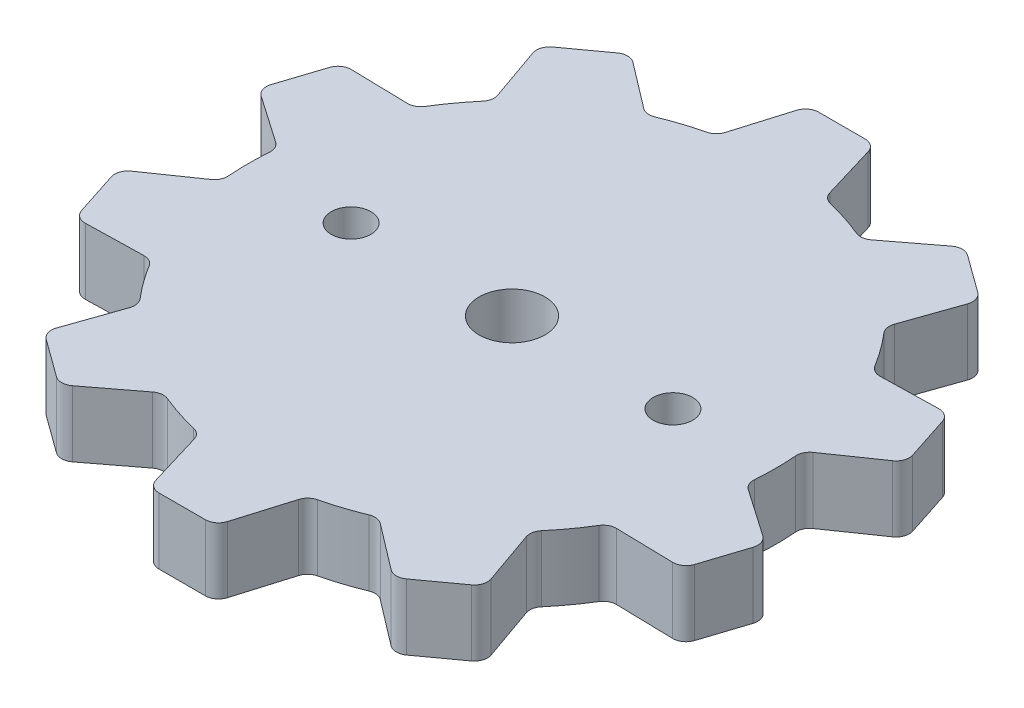
SolidWorks part; units mm, degrees
ref_plane "Front Plane" through (0, 0, 0) normal (0, 0, 1) x (1, 0, 0)
ref_plane "Top Plane" through (0, 0, 0) normal (0, 1, 0) x (1, 0, 0)
ref_plane "Right Plane" through (0, 0, 0) normal (1, 0, 0) x (0, 0, -1)
sketch "Sketch1" plane through (0, 0, 0) normal (0, 1, 0) x (1, 0, 0)
  line L0 (12.6721, 21.6949) -> (8.5196, 18.5315)
  line L1 (0, 25) -> (-2.5, 25)
  line L2 (0, 25) -> (2.5, 25)
  line L3 (14.6946, 20.2254) -> (12.6721, 21.6949)
  line L4 (14.6946, 20.2254) -> (16.7172, 18.756)
  line L5 (-2.5, 25) -> (-4, 20)
  line L6 (2.5, 25) -> (4, 20)
  line L7 (-4, 20) -> (-4.1293, 19.5691)
  line L8 (16.7172, 18.756) -> (14.9918, 13.8292)
  line L9 (14.9918, 13.8292) -> (14.8431, 13.4046)
  line L10 (4, 20) -> (4.1293, 19.5691)
  line L11 (8.5196, 18.5315) -> (8.1618, 18.2588)
  line L12 (23.0039, 10.1031) -> (17.7851, 9.9846)
  line L13 (23.7764, 7.7254) -> (23.0039, 10.1031)
  line L14 (23.7764, 7.7254) -> (24.549, 5.3478)
  line L15 (24.549, 5.3478) -> (20.2572, 2.3761)
  line L16 (20.2572, 2.3761) -> (19.8873, 2.12)
  line L17 (17.7851, 9.9846) -> (17.3353, 9.9744)
  line L18 (24.549, -5.3478) -> (20.2572, -2.3761)
  line L19 (23.7764, -7.7254) -> (24.549, -5.3478)
  line L20 (23.7764, -7.7254) -> (23.0039, -10.1031)
  line L21 (23.0039, -10.1031) -> (17.7851, -9.9846)
  line L22 (17.7851, -9.9846) -> (17.3353, -9.9744)
  line L23 (20.2572, -2.3761) -> (19.8873, -2.12)
  line L24 (16.7172, -18.756) -> (14.9918, -13.8292)
  line L25 (14.6946, -20.2254) -> (16.7172, -18.756)
  line L26 (14.6946, -20.2254) -> (12.6721, -21.6949)
  line L27 (12.6721, -21.6949) -> (8.5196, -18.5315)
  line L28 (8.5196, -18.5315) -> (8.1618, -18.2588)
  line L29 (14.9918, -13.8292) -> (14.8431, -13.4046)
  line L30 (2.5, -25) -> (4, -20)
  line L31 (0, -25) -> (2.5, -25)
  line L32 (0, -25) -> (-2.5, -25)
  line L33 (-2.5, -25) -> (-4, -20)
  line L34 (-4, -20) -> (-4.1293, -19.5691)
  line L35 (4, -20) -> (4.1293, -19.5691)
  line L36 (-12.6721, -21.6949) -> (-8.5196, -18.5315)
  line L37 (-14.6946, -20.2254) -> (-12.6721, -21.6949)
  line L38 (-14.6946, -20.2254) -> (-16.7172, -18.756)
  line L39 (-16.7172, -18.756) -> (-14.9918, -13.8292)
  line L40 (-14.9918, -13.8292) -> (-14.8431, -13.4046)
  line L41 (-8.5196, -18.5315) -> (-8.1618, -18.2588)
  line L42 (-23.0039, -10.1031) -> (-17.7851, -9.9846)
  line L43 (-23.7764, -7.7254) -> (-23.0039, -10.1031)
  line L44 (-23.7764, -7.7254) -> (-24.549, -5.3478)
  line L45 (-24.549, -5.3478) -> (-20.2572, -2.3761)
  line L46 (-20.2572, -2.3761) -> (-19.8873, -2.12)
  line L47 (-17.7851, -9.9846) -> (-17.3353, -9.9744)
  line L48 (-24.549, 5.3478) -> (-20.2572, 2.3761)
  line L49 (-23.7764, 7.7254) -> (-24.549, 5.3478)
  line L50 (-23.7764, 7.7254) -> (-23.0039, 10.1031)
  line L51 (-23.0039, 10.1031) -> (-17.7851, 9.9846)
  line L52 (-17.7851, 9.9846) -> (-17.3353, 9.9744)
  line L53 (-20.2572, 2.3761) -> (-19.8873, 2.12)
  line L54 (-16.7172, 18.756) -> (-14.9918, 13.8292)
  line L55 (-14.6946, 20.2254) -> (-16.7172, 18.756)
  line L56 (-14.6946, 20.2254) -> (-12.6721, 21.6949)
  line L57 (-12.6721, 21.6949) -> (-8.5196, 18.5315)
  line L58 (-8.5196, 18.5315) -> (-8.1618, 18.2588)
  line L59 (-14.9918, 13.8292) -> (-14.8431, 13.4046)
  circle A0 centre (0, 0) radius 20
  circle A1 centre (0, 0) radius 20
  circle A2 centre (0, 0) radius 20
  circle A3 centre (0, 0) radius 20
  circle A4 centre (0, 0) radius 20
  circle A5 centre (0, 0) radius 20
  circle A6 centre (0, 0) radius 20
  circle A7 centre (0, 0) radius 20
  circle A8 centre (0, 0) radius 20
  circle A9 centre (0, 0) radius 20
  point P93 (0, 0)
  dimension "D1" = 10
extrude "Boss-Extrude1" add sketch "Sketch1" along normal blind 5
sketch "Sketch2" plane through (0, 5, 0) normal (0, 1, 0) x (1, 0, 0)
  circle A0 centre (0, 0) radius 2.5
extrude "Cut-Extrude1" cut sketch "Sketch2" against normal blind 5
fillet "Fillet1" radius 1 20 edges at (-4.1293, 2.5, 19.5691) (-8.1618, 2.5, 18.2588) (-14.8431, 2.5, 13.4046) (-17.3353, 2.5, 9.9744) (-19.8873, 2.5, 2.12) (-19.8873, 2.5, -2.12) (-17.3353, 2.5, -9.9744) (-14.8431, 2.5, -13.4046) (-8.1618, 2.5, -18.2588) (-4.1293, 2.5, -19.5691) (4.1293, 2.5, -19.5691) (8.1618, 2.5, -18.2588) (14.8431, 2.5, -13.4046) (17.3353, 2.5, -9.9744) (19.8873, 2.5, -2.12) (19.8873, 2.5, 2.12) (17.3353, 2.5, 9.9744) (14.8431, 2.5, 13.4046) (8.1618, 2.5, 18.2588) (4.1293, 2.5, 19.5691)
fillet "Fillet2" radius 1 20 edges at (-12.6721, 2.5, 21.6949) (-16.7172, 2.5, 18.756) (-23.0039, 2.5, 10.1031) (-24.549, 2.5, 5.3478) (-24.549, 2.5, -5.3478) (-23.0039, 2.5, -10.1031) (-16.7172, 2.5, -18.756) (-12.6721, 2.5, -21.6949) (-2.5, 2.5, -25) (2.5, 2.5, -25) (12.6721, 2.5, -21.6949) (16.7172, 2.5, -18.756) (23.0039, 2.5, -10.1031) (24.549, 2.5, -5.3478) (24.549, 2.5, 5.3478) (23.0039, 2.5, 10.1031) (-2.5, 2.5, 25) (2.5, 2.5, 25) (12.6721, 2.5, 21.6949) (16.7172, 2.5, 18.756)
sketch "Sketch3" plane through (0, 5, 0) normal (0, 1, 0) x (1, 0, 0)
  line L0 (0, 31.3887) -> (0, -35.9377) construction
  line L1 (48.2743, 0) -> (-42.9899, 0) construction
sketch "Sketch4" plane through (0, 5, 0) normal (0, 1, 0) x (1, 0, 0)
  point P0 (12.2, 0)
  point P1 (-12.2, 0)
  point P2 (0, 0)
  point P4 (0, 0)
  dimension "D1" = 12.2
  dimension "D2" = 12.2
hole_wizard "Ø3.0mm Dowel Hole1" positions "Sketch5" profile "Sketch6" hole size "Ø3.0" standard "ANSI Metric" end condition through all
sketch "Sketch5" plane through (0, 5, 0) normal (0, 1, 0) x (1, 0, 0)
  point P0 (12.2, 0)
  point P3 (-12.2, 0)
sketch "Sketch6" plane through (12.2, 5, 0) normal (1, 0, 0) x (0, 0, 1)
  line L0 (0, 0) -> (0, 5)
  line L1 (0, 5) -> (1.5, 5)
  line L2 (1.5, 5) -> (1.5, 0)
  line L5 (1.5, 0) -> (0, 0)
  line L11 (0, -6.35) -> (0, 107.95) construction
  dimension "Thru Hole Dia." = 3
  dimension "Thru Hole Depth" = 5
